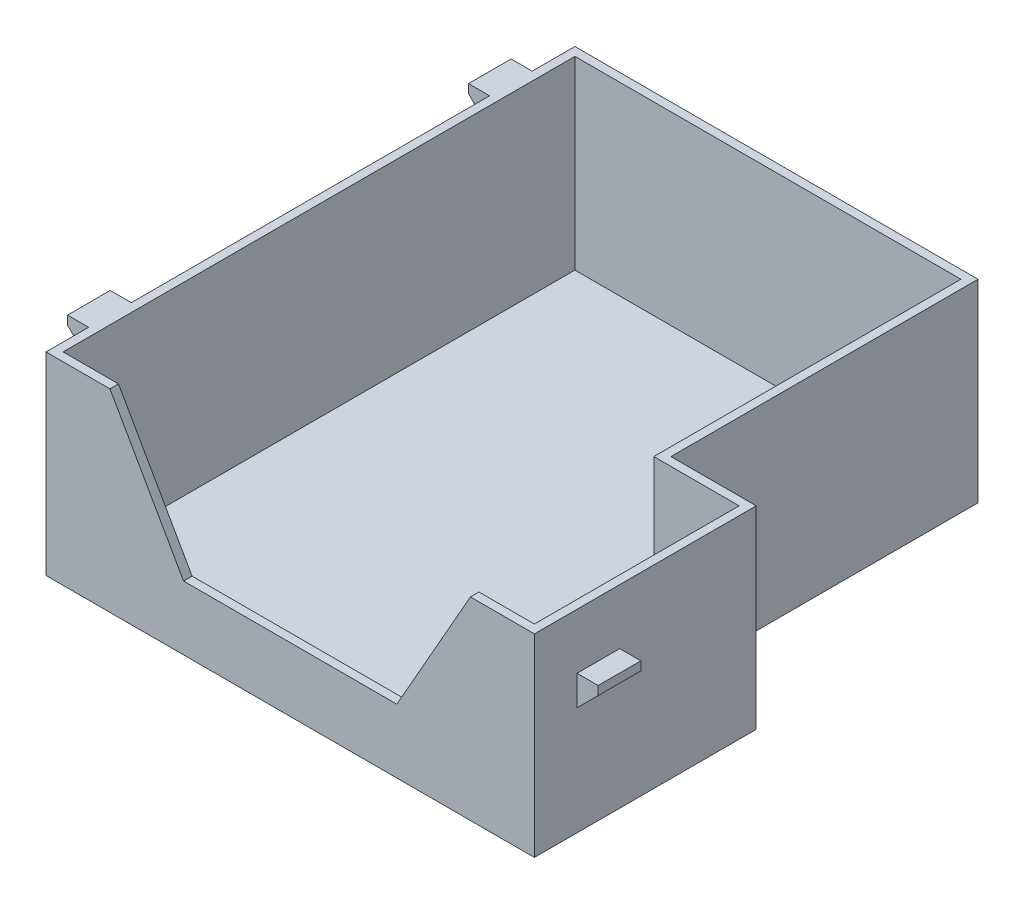
SolidWorks part; units mm, degrees
ref_plane "Plano frontal" through (0, 0, 0) normal (0, 0, 1) x (1, 0, 0)
ref_plane "Plano superior" through (0, 0, 0) normal (0, 1, 0) x (1, 0, 0)
ref_plane "Plano direito" through (0, 0, 0) normal (1, 0, 0) x (0, 0, -1)
sketch "Esboço1" plane through (0, 0, 0) normal (0, 1, 0) x (1, 0, 0)
  line L0 (57.25, -12) -> (37.25, -12)
  line L1 (-57.25, -62) -> (57.25, -62)
  line L2 (-57.25, -62) -> (-57.25, 62)
  line L3 (-57.25, 62) -> (37.25, 62)
  line L4 (57.25, -62) -> (57.25, -12)
  line L7 (37.25, -12) -> (37.25, 62)
  point P0 (0, 0)
  point P1 (0, -62)
  point P8 (-57.25, 0)
  dimension "D1" = 114.5
  dimension "D2" = 124
  dimension "D3" = 50
  dimension "D4" = 20
extrude "Ressalto-extrusão1" add sketch "Esboço1" along normal blind 2
sketch "Esboço2" plane through (0, 0, -62) normal (0, 0, -1) x (-1, 0, 0)
  line L21 (-37.25, 0) -> (57.25, 0)
  line L22 (-37.25, 0) -> (-37.25, 45.4)
  line L23 (-37.25, 45.4) -> (57.25, 45.4)
  line L24 (57.25, 0) -> (57.25, 45.4)
  dimension "D1" = 45.4
extrude "Ressalto-extrusão2" add sketch "Esboço2" against normal blind 2
sketch "Esboço3" plane through (0, 0, 62) normal (0, 0, 1) x (1, 0, 0)
  line L22 (-57.25, 0) -> (-57.25, 45.4)
  line L23 (-57.25, 45.4) -> (-42.25, 45.4)
  line L24 (-57.25, 45.4) -> (37.25, 45.4) construction
  line L25 (-42.25, 45.4) -> (-25, 15)
  line L26 (-25, 15) -> (25, 15)
  line L27 (25, 15) -> (42.25, 45.4)
  line L28 (42.25, 45.4) -> (57.25, 45.4)
  line L29 (57.25, 45.4) -> (57.25, 0)
  line L30 (57.25, 0) -> (-57.25, 0)
  dimension "D1" = 50
  dimension "D2" = 15
  dimension "D3" = 15
extrude "Ressalto-extrusão3" add sketch "Esboço3" against normal blind 2
sketch "Esboço4" plane through (-57.25, 0, 0) normal (-1, 0, 0) x (0, 0, 1)
  line L9 (-62, 0) -> (62, 0)
  line L10 (-62, 0) -> (-62, 45.4)
  line L11 (-62, 45.4) -> (62, 45.4)
  line L12 (62, 0) -> (62, 45.4)
extrude "Ressalto-extrusão4" add sketch "Esboço4" against normal blind 2
sketch "Esboço5" plane through (57.25, 0, 0) normal (1, 0, 0) x (0, 0, -1)
  line L0 (-60, 45.4) -> (60, 45.4) construction
  line L1 (-62, 0) -> (-12, 0)
  line L2 (-62, 0) -> (-62, 45.4)
  line L3 (-62, 45.4) -> (-12, 45.4)
  line L4 (-12, 0) -> (-12, 45.4)
  dimension "D1" = 50
extrude "Ressalto-extrusão5" add sketch "Esboço5" against normal blind 2
sketch "Esboço6" plane through (0, 0, 62) normal (0, 0, 1) x (1, 0, 0)
  line L5 (57.25, 25.4) -> (62.1997, 30.3497)
  line L7 (57.25, 45.4) -> (57.25, 0) construction
  line L8 (62.1997, 30.3497) -> (62.1997, 32.4)
  line L9 (62.1997, 32.4) -> (57.25, 32.4)
  line L10 (57.25, 32.4) -> (57.25, 25.4)
  line L11 (-57.25, 0) -> (57.25, 0) construction
  dimension "D1" = 25.4
  dimension "D2" = 45
  dimension "D3" = 7
  dimension "D4" = 7
extrude "Ressalto-extrusão6" add sketch "Esboço6" against normal blind 10 from offset 10 offset against normal yes
sketch "Esboço8" plane through (0, 0, 62) normal (0, 0, 1) x (1, 0, 0)
  line L0 (-57.25, 38.4) -> (-62.1997, 43.3497)
  line L1 (-57.25, 45.4) -> (-57.25, 0) construction
  line L2 (-62.1997, 43.3497) -> (-62.1997, 45.4)
  line L3 (-62.1997, 45.4) -> (-57.25, 45.4)
  line L4 (-57.25, 45.4) -> (-57.25, 38.4)
  line L5 (-57.25, 0) -> (57.25, 0) construction
  dimension "D1" = 38.4
  dimension "D2" = 45
  dimension "D3" = 7
  dimension "D4" = 7
extrude "Ressalto-extrusão7" add sketch "Esboço8" against normal blind 10 from offset 10 offset against normal yes
sketch "Esboço10" plane through (0, 0, -62) normal (0, 0, -1) x (-1, 0, 0)
  line L4 (57.25, 45.4) -> (57.25, 38.4)
  line L5 (57.25, 38.4) -> (62.1997, 43.3497)
  line L6 (62.1997, 43.3497) -> (62.1997, 45.4)
  line L7 (62.1997, 45.4) -> (57.25, 45.4)
  line L8 (57.25, 45.4) -> (57.25, 38.4)
  line L9 (57.25, 38.4) -> (62.1997, 43.3497)
  line L10 (62.1997, 43.3497) -> (62.1997, 45.4)
  line L11 (62.1997, 45.4) -> (57.25, 45.4)
  dimension "D1" = 0
extrude "Ressalto-extrusão8" add sketch "Esboço10" against normal blind 10 from offset 10 offset against normal yes
sketch "Esboço11" plane through (0, 0, 12) normal (0, 0, -1) x (-1, 0, 0)
  line L1 (-57.25, 0) -> (-35.25, 0)
  line L2 (-57.25, 0) -> (-57.25, 45.4)
  line L3 (-57.25, 45.4) -> (-35.25, 45.4)
  line L4 (-35.25, 0) -> (-35.25, 45.4)
  dimension "D1" = 22
  dimension "D2" = 45.4
extrude "Ressalto-extrusão9" add sketch "Esboço11" along normal blind 2
sketch "Esboço14" plane through (37.25, 0, 0) normal (1, 0, 0) x (0, 0, -1)
  line L1 (62, 0) -> (-10, 0)
  line L2 (62, 0) -> (62, 45.4)
  line L3 (62, 45.4) -> (-10, 45.4)
  line L4 (-10, 0) -> (-10, 45.4)
extrude "Ressalto-extrusão14" add sketch "Esboço14" against normal blind 2
